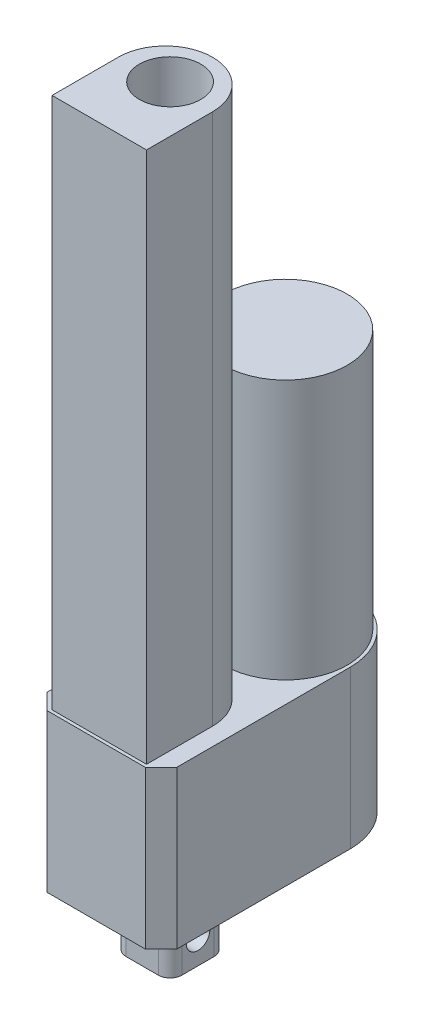
SolidWorks part; units mm, degrees
ref_plane "Front Plane" through (0, 0, 0) normal (0, 0, 1) x (1, 0, 0)
ref_plane "Top Plane" through (0, 0, 0) normal (0, 1, 0) x (1, 0, 0)
ref_plane "Right Plane" through (0, 0, 0) normal (1, 0, 0) x (0, 0, -1)
sketch "Sketch1" plane through (0, 0, 0) normal (0, 1, 0) x (1, 0, 0)
  line L0 (-50.8362, -27.6557) -> (-45.7562, -32.7357)
  line L1 (-29.9066, 49.3063) -> (-29.8558, 49.3063)
  line L2 (-50.8362, 28.3767) -> (-50.8362, -27.6557)
  line L3 (-45.7562, -32.7357) -> (-14.0062, -32.7357)
  line L4 (-8.9262, 28.3767) -> (-8.9262, -27.6557)
  line L5 (-14.0062, -32.7357) -> (-8.9262, -27.6557)
  arc A0 (-29.9066, 49.3063) -> (-50.8362, 28.3767) centre (-29.9066, 28.3767) ccw
  arc A1 (-29.8558, 49.3063) -> (-8.9262, 28.3767) centre (-29.8558, 28.3767) cw
  point P1 (-8.9262, -32.7357)
  point P2 (-50.8362, -32.7357)
  point P8 (-8.9262, 49.3063)
  dimension "D3" = 20.9296
  dimension "D1" = 41.91
  dimension "D2" = 82.042
  dimension "D4" = 5.08
  dimension "D5" = 45
  dimension "D6" = 5.08
  dimension "D7" = 45
extrude "Boss-Extrude1" add sketch "Sketch1" along normal blind 50.8
sketch "Sketch2" plane through (0, 50.8, 0) normal (0, 1, 0) x (1, 0, 0)
  line L0 (-8.9262, -27.6557) -> (-8.9262, 28.3767) construction
  line L1 (-29.8558, 49.3063) -> (-29.9066, 49.3063) construction
  circle A0 centre (-29.8812, 28.3513) radius 19.939
  dimension "D1" = 39.878
  dimension "D2" = 20.955
  dimension "D3" = 20.955
extrude "Boss-Extrude2" add sketch "Sketch2" along normal blind 83.82
sketch "Sketch3" plane through (0, 50.8, 0) normal (0, 1, 0) x (1, 0, 0)
  line L2 (-45.1212, -31.7079) -> (-14.6412, -31.7079)
  line L3 (-45.1212, -31.7079) -> (-45.1212, -10.3719)
  line L5 (-14.6412, -31.7079) -> (-14.6412, -10.3719)
  arc A0 (-45.1212, -10.3719) -> (-14.6412, -10.3719) centre (-29.8812, -10.3719) cw
  dimension "D1" = 30.48
  dimension "D2" = 21.336
extrude "Boss-Extrude3" add sketch "Sketch3" along normal blind 171.704
sketch "Sketch4" plane through (0, 0, 0) normal (0, -1, 0) x (-1, 0, 0)
  line L0 (29.8812, -32.7357) -> (29.8812, 45.1768) construction
  line L1 (24.6742, 0.1573) -> (35.0882, 0.1573)
  line L2 (20.8642, -3.6527) -> (20.8642, -14.0667)
  line L3 (24.6742, -17.8767) -> (35.0882, -17.8767)
  line L4 (38.8982, -3.6527) -> (38.8982, -14.0667)
  line L5 (45.7562, -32.7357) -> (14.0062, -32.7357) construction
  arc A0 (35.0882, 0.1573) -> (38.8982, -3.6527) centre (35.0882, -3.6527) cw
  arc A1 (35.0882, -17.8767) -> (38.8982, -14.0667) centre (35.0882, -14.0667) ccw
  arc A2 (20.8642, -14.0667) -> (24.6742, -17.8767) centre (24.6742, -14.0667) ccw
  arc A3 (24.6742, 0.1573) -> (20.8642, -3.6527) centre (24.6742, -3.6527) ccw
  point P8 (29.8812, 0.1573)
  point P13 (38.8982, -17.8767)
  point P16 (20.8642, -17.8767)
  point P19 (20.8642, 0.1573)
  dimension "D4" = 3.81
  dimension "D1" = 18.034
  dimension "D2" = 18.034
  dimension "D3" = 14.859
extrude "Boss-Extrude4" add sketch "Sketch4" along normal blind 20.066
sketch "Sketch5" plane through (-38.8982, 0, 0) normal (-1, 0, 0) x (0, 0, 1)
  line L0 (14.0667, 0) -> (3.6527, 0) construction
  line L1 (8.8597, -20.066) -> (8.8597, 0) construction
  line L2 (14.0667, -20.066) -> (3.6527, -20.066) construction
  circle A0 centre (8.8597, -11.938) radius 3.81
  dimension "D1" = 7.62
  dimension "D2" = 11.938
extrude "Cut-Extrude1" cut sketch "Sketch5" against normal blind 20.066
sketch3d "3DSketch1"
  line L0 (-38.8982, -20.066, 8.8597) -> (-20.8642, -20.066, 8.8597) construction
  line L1 (-38.8982, -20.066, 14.0667) -> (-38.8982, -20.066, 3.6527) construction
  line L2 (-20.8642, -20.066, 3.6527) -> (-20.8642, -20.066, 14.0667) construction
  line L3 (-29.8812, -20.066, -0.1573) -> (-29.8812, -20.066, 17.8767) construction
  line L4 (-35.0882, -20.066, -0.1573) -> (-24.6742, -20.066, -0.1573) construction
  line L5 (-24.6742, -20.066, 17.8767) -> (-35.0882, -20.066, 17.8767) construction
  line L6 (-29.8812, -20.066, 8.8597) -> (-29.8812, 222.504, 8.8597)
sketch "Sketch6" plane through (0, 222.504, 0) normal (0, 1, 0) x (1, 0, 0)
  circle A0 centre (-29.8812, -8.8597) radius 9.906
  dimension "D1" = 19.812
extrude "Cut-Extrude2" cut sketch "Sketch6" against normal blind 127
